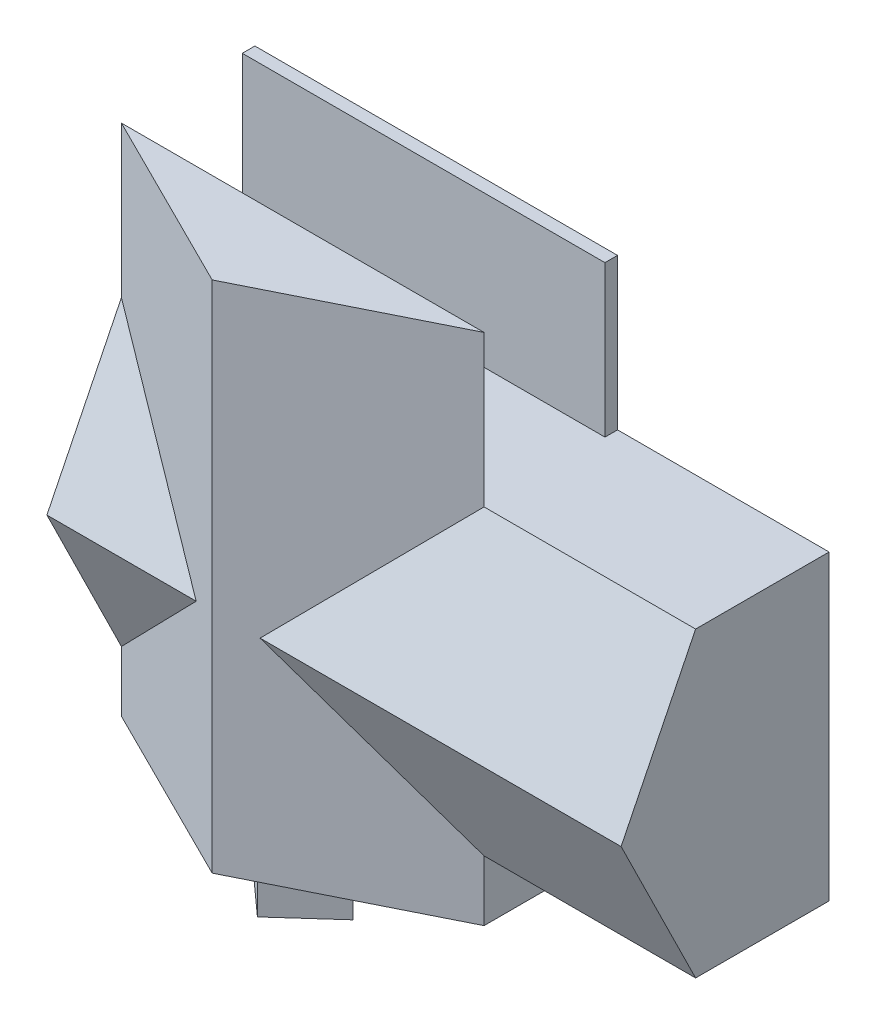
SolidWorks part; units mm, degrees
ref_plane "Front Plane" through (0, 0, 0) normal (0, 0, 1) x (1, 0, 0)
ref_plane "Top Plane" through (0, 0, 0) normal (0, 1, 0) x (1, 0, 0)
ref_plane "Right Plane" through (0, 0, 0) normal (1, 0, 0) x (0, 0, -1)
sketch "Sketch3" plane through (0, 0, 0) normal (0, 0, 1) x (1, 0, 0)
  line L0 (152.4, 152.4) -> (4550.005, 152.4)
  line L1 (0, 0) -> (11582.4, 0)
  line L2 (0, 0) -> (0, 6096)
  line L3 (0, 6096) -> (11582.4, 6096)
  line L4 (11582.4, 0) -> (11582.4, 6096)
  line L5 (4550.005, 152.4) -> (4550.005, 2596.7986)
  line L6 (4550.005, 2596.7986) -> (5842, 2596.7986)
  line L7 (11582.4, 6096) -> (7620, 6096) construction
  line L8 (7620, 6096) -> (5842, 6096) construction
  line L9 (5842, 5943.6) -> (5842, 3511.1986)
  line L10 (5943.6, 3511.1986) -> (10284.7543, 3511.1986)
  line L11 (7620, 5943.6) -> (7620, 3612.7986)
  line L12 (4550.005, 2596.7986) -> (5842, 2596.7986) construction
  line L13 (7315.2, 2495.1986) -> (7315.2, 152.4)
  line L14 (5842, 3511.1986) -> (5842, 2596.7986)
  line L15 (10386.3543, 3511.1986) -> (10386.3543, 2596.7986)
  line L16 (9786.5812, 3511.1986) -> (9786.5812, 2596.7986) construction
  line L17 (0, 6096) -> (0, 9448.8) construction
  line L18 (0, 9448.8) -> (6388.492, 9448.8) construction
  line L19 (6388.492, 9448.8) -> (6388.492, 6096) construction
  line L20 (11430, 152.4) -> (11430, 2495.1986)
  line L21 (3310.1163, 2590.8) -> (0, 2590.8) construction
  line L22 (152.4, 5943.6) -> (5842, 5943.6)
  line L23 (152.4, 152.4) -> (152.4, 5943.6)
  line L24 (4651.605, 152.4) -> (4651.605, 2495.1986)
  line L25 (4651.605, 2495.1986) -> (7315.2, 2495.1986)
  line L26 (7416.8, 2495.1986) -> (7416.8, 152.4)
  line L27 (10284.7543, 3511.1986) -> (10284.7543, 2596.7986)
  line L28 (5943.6, 3612.7986) -> (7620, 3612.7986)
  line L29 (5943.6, 5943.6) -> (5943.6, 3612.7986)
  line L30 (7721.6, 5943.6) -> (7721.6, 3612.7986)
  line L31 (7620, 6096) -> (7620, 3505.2) construction
  line L32 (7721.6, 6096) -> (7721.6, 3505.2) construction
  line L33 (5842, 6096) -> (5842, 3511.1986) construction
  line L34 (5943.6, 6096) -> (5943.6, 3511.1986) construction
  line L35 (5943.6, 5943.6) -> (7620, 5943.6)
  line L36 (152.4, 5943.6) -> (11430, 5943.6) construction
  line L37 (7721.6, 5943.6) -> (11430, 5943.6)
  line L38 (5842, 3612.7986) -> (11582.4, 3612.7986) construction
  line L39 (7721.6, 3612.7986) -> (11430, 3612.7986)
  line L40 (11430, 3612.7986) -> (11430, 5943.6)
  line L41 (11430, 152.4) -> (11430, 5943.6) construction
  line L42 (5842, 3511.1986) -> (11582.4, 3511.1986) construction
  line L43 (10386.3543, 3511.1986) -> (11430, 3511.1986)
  line L44 (10386.3543, 2596.7986) -> (11430, 2596.7986)
  line L45 (4550.005, 2596.7986) -> (11582.4, 2596.7986) construction
  line L46 (11430, 2596.7986) -> (11430, 3511.1986)
  line L47 (4651.605, 2495.1986) -> (11582.4, 2495.1986) construction
  line L48 (7315.2, 2596.7986) -> (7315.2, 0) construction
  line L49 (7416.8, 2596.7986) -> (7416.8, 0) construction
  line L50 (7416.8, 2495.1986) -> (11430, 2495.1986)
  line L51 (7416.8, 152.4) -> (11430, 152.4)
  line L52 (152.4, 152.4) -> (11430, 152.4) construction
  line L53 (4550.005, 0) -> (4550.005, 2596.7986) construction
  line L54 (4651.605, 0) -> (4651.605, 2495.1986) construction
  line L55 (4651.605, 152.4) -> (7315.2, 152.4)
  line L56 (5943.6, 3511.1986) -> (5943.6, 2596.7986)
  line L57 (5943.6, 2596.7986) -> (10284.7543, 2596.7986)
  line L58 (5943.6, 2596.7986) -> (7315.2, 2596.7986) construction
  dimension "D1" = 11582.4
  dimension "D2" = 6096
  dimension "D4" = 3962.4
  dimension "D5" = 1778
  dimension "D7" = 914.4
  dimension "D8" = 152.4
  dimension "D9" = 101.6
  dimension "D10" = 101.6
  dimension "D11" = 101.6
  dimension "D12" = 101.6
  dimension "D13" = 101.6
extrude "Boss-Extrude1" add sketch "Sketch3" along normal blind 2438.4 contours L1 L4 L3 L2 L55 L24 L25 L13 L51 L26 L50 L20 L46 L44 L15 L43 L40 L39 L30 L37 L10 L27 L6 L5 L0 L23 L22 L9 L29 L35 L11 L28
sketch "Sketch4" plane through (0, 0, 0) normal (0, 0, -1) x (-1, 0, 0)
  line L1 (-11582.4, 6096) -> (0, 6096)
  line L2 (-11582.4, 6096) -> (-11582.4, 0)
  line L3 (-11582.4, 0) -> (0, 0)
  line L4 (0, 6096) -> (0, 0)
extrude "Boss-Extrude2" add sketch "Sketch4" along normal blind 254
sketch "Sketch5" plane through (0, 0, 0) normal (0, 0, 1) x (1, 0, 0)
  line L1 (3330.805, 2596.7986) -> (152.4, 2596.7986)
  line L2 (152.4, 152.4) -> (152.4, 5943.6) construction
  line L3 (152.4, 2596.7986) -> (152.4, 2495.1986)
  line L4 (152.4, 152.4) -> (152.4, 5943.6) construction
  line L5 (152.4, 2495.1986) -> (3330.805, 2495.1986)
  line L6 (3330.805, 2495.1986) -> (3330.805, 2596.7986)
extrude "Boss-Extrude3" add sketch "Sketch5" along normal blind 1016
sketch "Sketch6" plane through (0, 0, 0) normal (-1, 0, 0) x (0, 0, 1)
  line L0 (2438.4, 6096) -> (2438.4, 0)
  line L1 (2438.4, 6096) -> (3941.5073, 3048)
  line L2 (2438.4, 3048) -> (3941.5073, 3048) construction
  line L3 (3941.5073, 3048) -> (2438.4, 0)
  dimension "D1" = 26.25
extrude "Boss-Extrude4" add sketch "Sketch6" against normal up to surface (11582.4 mm away) up to face at (11582.4, 3048, 1092.2)
sketch "Sketch7" plane through (0, 6096, 0) normal (0, 1, 0) x (1, 0, 0)
  line L0 (0, 254) -> (7315.2, 254) construction
  line L1 (0, 254) -> (11582.4, 254) construction
  line L2 (7315.2, 254) -> (7315.2, -2438.4) construction
  line L3 (0, -2438.4) -> (11582.4, -2438.4) construction
  line L4 (7937.8596, -2438.4) -> (5791.2, -3941.5073)
  line L5 (11582.4, -3941.5073) -> (0, -3941.5073) construction
  line L6 (5791.2, -3941.5073) -> (5791.2, -2438.4) construction
  line L7 (3644.5404, -2438.4) -> (5791.2, -3941.5073)
  line L8 (7937.8596, -2438.4) -> (3644.5404, -2438.4)
  dimension "D1" = 55
sketch "Sketch8" plane through (0, 0, -254) normal (0, 0, -1) x (-1, 0, 0)
  line L1 (0, 6096) -> (-7315.2, 6096)
  line L2 (0, 6096) -> (0, 9144)
  line L3 (0, 9144) -> (-7315.2, 9144)
  line L4 (-7315.2, 6096) -> (-7315.2, 9144)
  dimension "D1" = 7315.2
  dimension "D2" = 3048
extrude "Boss-Extrude6" add sketch "Sketch8" against normal blind 254 separate body
sketch "Sketch9" plane through (0, 0, 0) normal (-1, 0, 0) x (0, 0, 1)
  line L0 (2438.4, 0) -> (4693.0609, 4572)
  line L1 (2438.4, 0) -> (2438.4, 9144)
  line L2 (2438.4, 4572) -> (4693.0609, 4572) construction
  line L3 (2438.4, 9144) -> (4693.0609, 4572)
sketch "Sketch10" plane through (0, 9144, 0) normal (0, 1, 0) x (1, 0, 0)
  line L0 (7315.2, -2438.4) -> (0, -2438.4)
  line L1 (3644.5404, -2438.4) -> (3657.6, -4693.0609) construction
  line L2 (7315.2, -4693.0609) -> (0, -4693.0609) construction
  line L5 (7315.2, -2438.4) -> (3655.1104, -4263.2533)
  line L6 (3655.1104, -4263.2533) -> (0, -2438.4)
  dimension "D1" = 26.5
extrude "Boss-Extrude7" add sketch "Sketch10" against normal blind 10363.2
sketch "Sketch11" plane through (0, -967.2564, 1961.4019) normal (0, -0.4423, 0.8969) x (1, 0, 0)
  line L1 (5444.9184, 4256.1108) -> (2083.927, 4256.1108)
  line L2 (5444.9184, 4256.1108) -> (5444.9184, 5301.5124)
  line L3 (5444.9184, 5301.5124) -> (2083.927, 5301.5124)
  line L4 (2083.927, 4256.1108) -> (2083.927, 5301.5124)
extrude "Cut-Extrude1" [suppressed] cut sketch "Sketch11" along normal blind 6085.84
sketch "Sketch12" plane through (0, 0, -254) normal (0, 0, -1) x (-1, 0, 0)
  line L0 (0, 0) -> (0, -1219.2)
  line L1 (0, -1219.2) -> (-7315.2, -1219.2)
  line L2 (-7315.2, -1219.2) -> (-7315.2, 0)
  line L3 (-11582.4, 0) -> (0, 0) construction
  line L4 (-7315.2, 0) -> (0, 0)
extrude "Boss-Extrude8" add sketch "Sketch12" against normal blind 2692.4
sketch "Sketch14" plane through (0, 0, 0) normal (-1, 0, 0) x (0, 0, 1)
  line L0 (2916.7919, -235.9168) -> (4419.8992, 2812.0832)
  line L1 (2916.7919, -235.9168) -> (2299.5618, -1487.5356)
  line L2 (4419.8992, 2812.0832) -> (4384.9984, -1487.5356)
  line L3 (4384.9984, -1487.5356) -> (2299.5618, -1487.5356)
  line L6 (-254, 6096) -> (-254, -1219.2)
  line L7 (-254, -1219.2) -> (2438.4, -1219.2)
  line L8 (2438.4, -1219.2) -> (2438.4, 0)
  line L9 (2438.4, 0) -> (3941.5073, 3048)
  line L10 (3941.5073, 3048) -> (2438.4, 6096)
  line L11 (2438.4, 6096) -> (-254, 6096)
  line L15 (2438.4, 0) -> (3941.5073, 3048) construction
  dimension "D1" = 0
  dimension "D2" = 533.4
extrude "Cut-Extrude2" [suppressed] cut sketch "Sketch14" against normal blind 8897.366
sketch "Sketch15" plane through (0, -1219.2, 0) normal (0, -1, 0) x (1, 0, 0)
  line L0 (0, 2438.4) -> (7315.2, 2438.4) construction
  line L1 (3657.6, 2438.4) -> (3657.6, 3352.8) construction
  line L2 (2641.6, 2438.4) -> (4673.6, 2438.4)
  line L3 (4673.6, 2438.4) -> (3657.6, 3352.8)
  line L4 (3657.6, 3352.8) -> (2641.6, 2438.4)
  point P9 (3657.6, 2438.4)
extrude "Boss-Extrude9" add sketch "Sketch15" along normal blind 1219.2
